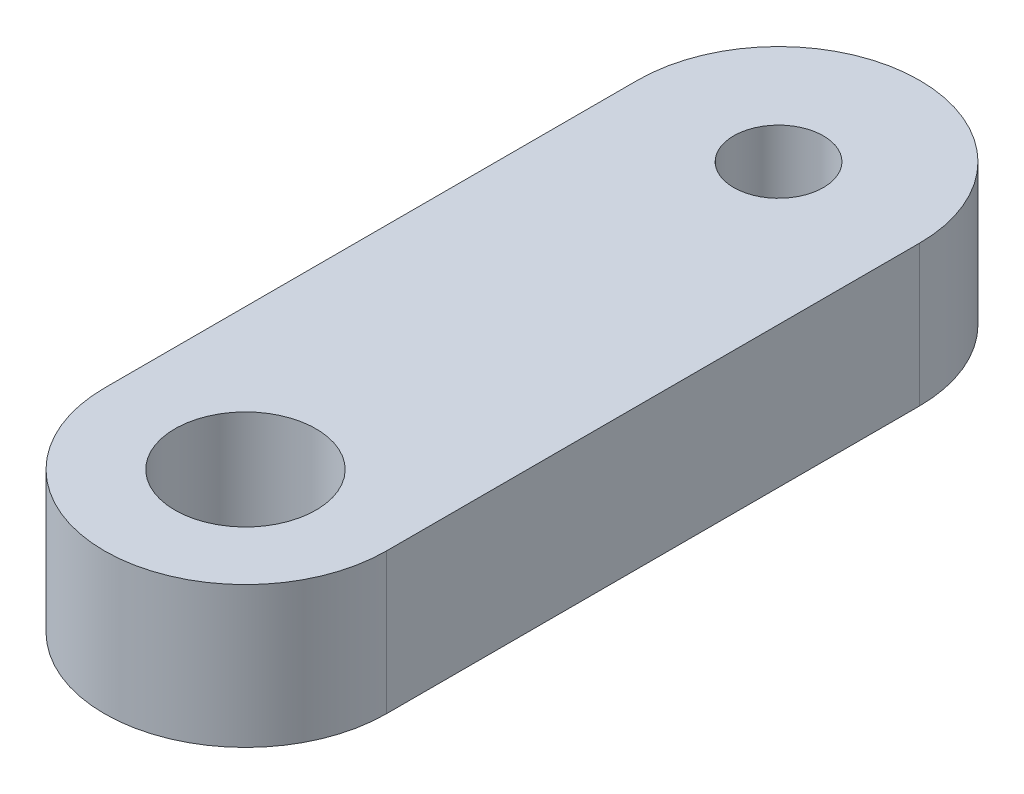
SolidWorks part; units mm, degrees
ref_plane "Front" through (0, 0, 0) normal (0, 0, 1) x (1, 0, 0)
ref_plane "Top" through (0, 0, 0) normal (0, 1, 0) x (1, 0, 0)
ref_plane "Right" through (0, 0, 0) normal (1, 0, 0) x (0, 0, -1)
sketch "Sketch1" plane through (0, 0, 0) normal (0, 1, 0) x (1, 0, 0)
  line L0 (0, 24) -> (0, 0) construction
  line L1 (6.35, 24) -> (6.35, 0)
  line L2 (-6.35, 24) -> (-6.35, 0)
  circle A0 centre (0, 0) radius 3.175
  arc A2 (6.35, 24) -> (-6.35, 24) centre (0, 24) ccw
  arc A3 (-6.35, 0) -> (6.35, 0) centre (0, 0) ccw
  point P5 (0, 12)
  dimension "D2" = 6.35
  dimension "D3" = 6.35
  dimension "D1" = 24
extrude "Boss-Extrude1" add sketch "Sketch1" along normal blind 6.35
hole_wizard "#10-32 Tapped Hole1" positions "Sketch2" profile "Sketch3" tap size "#10-32" standard "ANSI Inch" end condition through all
sketch "Sketch2" plane through (0, 6.35, 0) normal (0, 1, 0) x (1, 0, 0)
  point P0 (0, 24)
sketch "Sketch3" plane through (0, 6.35, -24) normal (1, 0, 0) x (0, 0, 1)
  line L0 (0, 0) -> (0, 6.35)
  line L1 (0, 6.35) -> (2.0193, 6.35)
  line L2 (2.0193, 6.35) -> (2.0193, 0)
  line L5 (2.0193, 0) -> (0, 0)
  line L11 (0, -6.35) -> (0, 107.95) construction
  dimension "Thru Tap Drill Dia." = 4.0386
  dimension "Thru Tap Drill Depth" = 6.35
cosmetic thread "Hole Thread1" parameters "D2"=4.826
